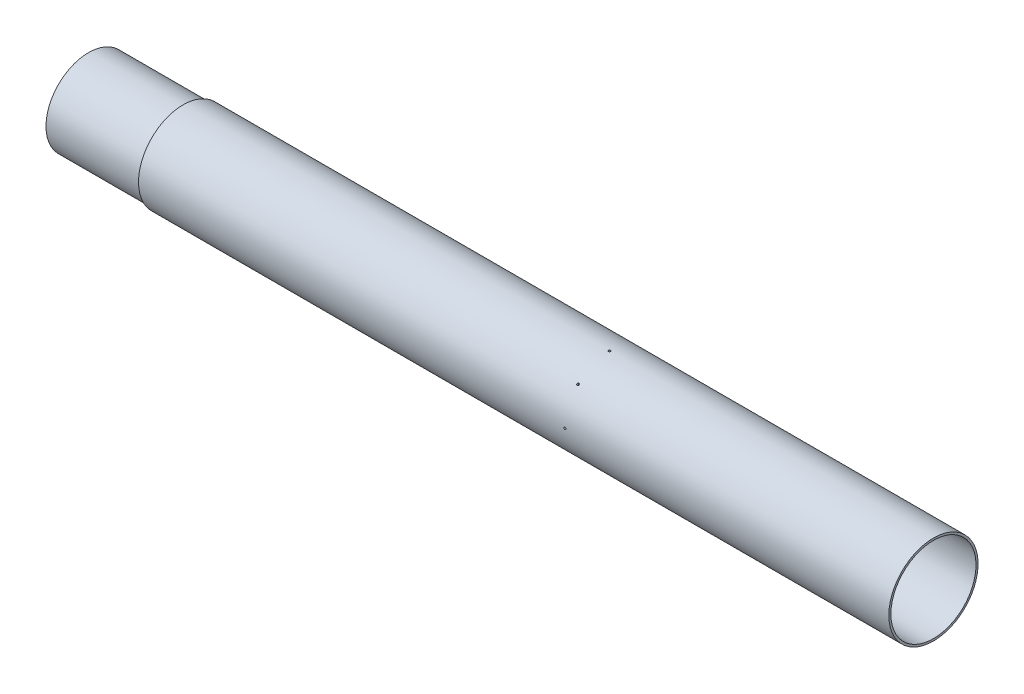
SolidWorks part; units mm, degrees
ref_plane "Front Plane" through (0, 0, 0) normal (0, 0, 1) x (1, 0, 0)
ref_plane "Top Plane" through (0, 0, 0) normal (0, 1, 0) x (1, 0, 0)
ref_plane "Right Plane" through (0, 0, 0) normal (1, 0, 0) x (0, 0, -1)
sketch "Sketch1" plane through (0, 0, 0) normal (0, 0, 1) x (1, 0, 0)
  line L0 (-1238.9107, 59.9364) -> (-2246.5566, 59.9364)
  line L1 (-2246.5566, 59.9364) -> (-2246.5566, 57.15)
  line L2 (-2246.5566, 57.15) -> (-2373.5566, 57.15)
  line L3 (-2373.5566, 57.15) -> (-2373.5566, 54.3636)
  line L4 (-2373.5566, 54.3636) -> (-2119.5566, 54.3636)
  line L5 (-2119.5566, 54.3636) -> (-2119.5566, 57.15)
  line L6 (-2119.5566, 57.15) -> (-1238.9107, 57.15)
  line L7 (-1238.9107, 57.15) -> (-1238.9107, 59.9364)
  line L8 (-2246.5566, 0) -> (-1840.7203, 0) construction
  dimension "D1" = 1007.6459
  dimension "D2" = 127
  dimension "D3" = 2.7864
  dimension "D4" = 2.7864
  dimension "D5" = 254
  dimension "D6" = 2.7864
  dimension "D7" = 57.15
revolve "Revolve1" add sketch "Sketch1" angle 360 about L8
ref_plane "Plane1" through (0, 0, -59.9364) normal (0, 0, -1) x (-1, 0, 0)
sketch "Sketch2" plane through (0, 0, -59.9364) normal (0, 0, -1) x (-1, 0, 0)
  line L0 (1238.9107, 59.9364) -> (1238.9107, -59.9364) construction
  circle A0 centre (1673.9107, 0) radius 1.4224
  dimension "D2" = 2.8448
  dimension "D1" = 435
extrude "Cut-Extrude1" cut sketch "Sketch2" against normal blind 20
pattern_circular "CirPattern1" count 8 over 360 about axis through (-1238.9107, 0, 0) along (-1, 0, 0) of "Cut-Extrude1"
